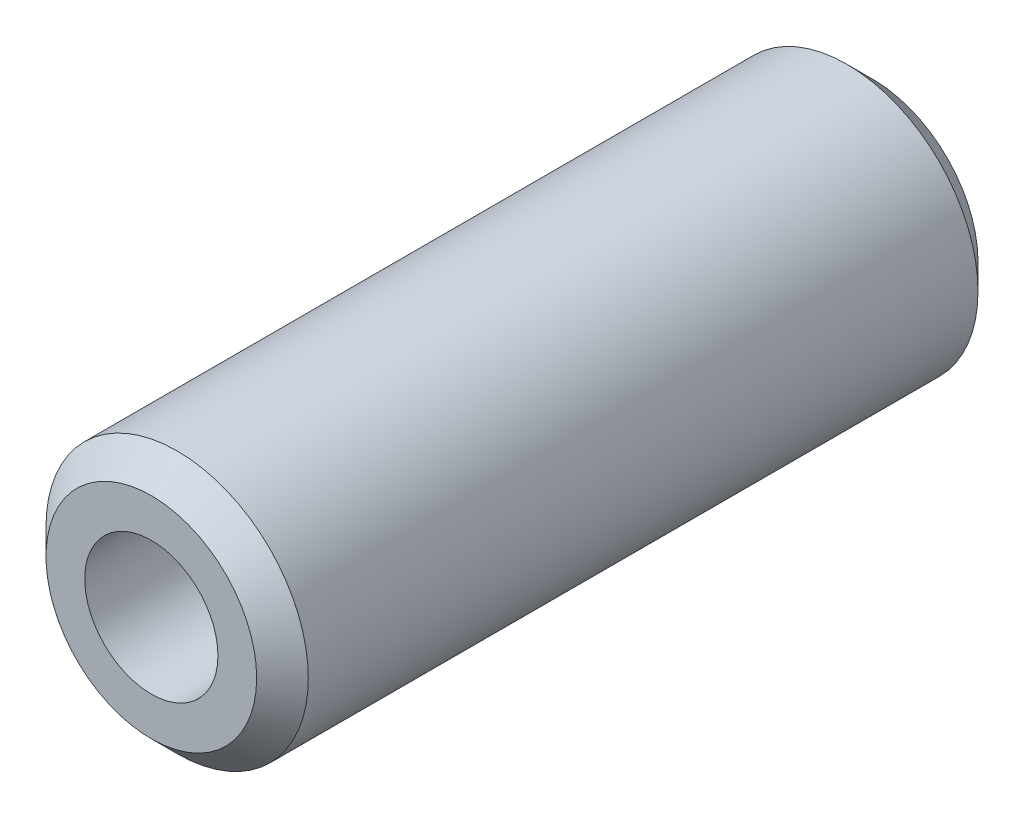
SolidWorks part; units mm, degrees
ref_plane "Front Plane" through (0, 0, 0) normal (0, 0, 1) x (1, 0, 0)
ref_plane "Top Plane" through (0, 0, 0) normal (0, 1, 0) x (1, 0, 0)
ref_plane "Right Plane" through (0, 0, 0) normal (1, 0, 0) x (0, 0, -1)
sketch "Sketch2" plane through (0, 0, 0) normal (0, 0, 1) x (1, 0, 0)
  circle A0 centre (0, 0) radius 12.7
  dimension "D1" = 25.4
extrude "Boss-Extrude1" add sketch "Sketch2" along normal blind 69.85
sketch "Sketch3" plane through (0, 0, 69.85) normal (0, 0, 1) x (1, 0, 0)
  circle A0 centre (0, 0) radius 6.45
  dimension "D1" = 12.9
extrude "Cut-Extrude1" cut sketch "Sketch3" against normal through all both and the other way through all contours A0
chamfer "Chamfer1" distance 2.5 angle 45 2 edges at (12.7, 0, 0) (12.7, 0, 69.85)
